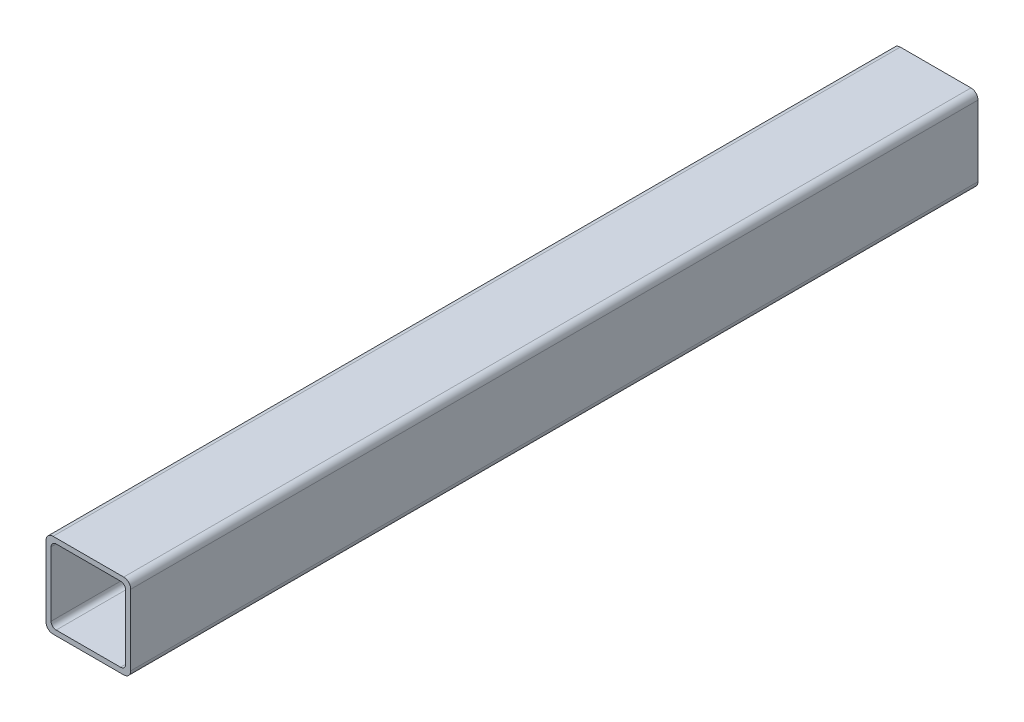
SolidWorks part; units mm, degrees
material "6061 Alloy"
ref_plane "Front Plane" through (0, 0, 0) normal (0, 0, 1) x (1, 0, 0)
ref_plane "Top Plane" through (0, 0, 0) normal (0, 1, 0) x (1, 0, 0)
ref_plane "Right Plane" through (0, 0, 0) normal (1, 0, 0) x (0, 0, -1)
ref_plane "Plane1" through (0, 0, -3683) normal (0, 0, -1) x (-1, 0, 0)
sketch "Sketch1" plane through (0, 0, -3683) normal (0, 0, -1) x (-1, 0, 0)
  line L0 (11.176, 9.652) -> (11.176, -9.652)
  line L1 (9.652, -11.176) -> (-9.652, -11.176)
  line L2 (-11.176, -9.652) -> (-11.176, 9.652)
  line L3 (-9.652, 11.176) -> (9.652, 11.176)
  line L4 (12.7, -10.5918) -> (12.7, 10.5918)
  line L5 (10.5918, 12.7) -> (-10.5918, 12.7)
  line L6 (-12.7, 10.5918) -> (-12.7, -10.5918)
  line L7 (-10.5918, -12.7) -> (10.5918, -12.7)
  arc A0 (11.176, -9.652) -> (9.652, -11.176) centre (9.652, -9.652) cw
  arc A1 (-9.652, -11.176) -> (-11.176, -9.652) centre (-9.652, -9.652) cw
  arc A2 (-11.176, 9.652) -> (-9.652, 11.176) centre (-9.652, 9.652) cw
  arc A3 (9.652, 11.176) -> (11.176, 9.652) centre (9.652, 9.652) cw
  arc A4 (12.7, 10.5918) -> (10.5918, 12.7) centre (10.5918, 10.5918) ccw
  arc A5 (-10.5918, 12.7) -> (-12.7, 10.5918) centre (-10.5918, 10.5918) ccw
  arc A6 (-12.7, -10.5918) -> (-10.5918, -12.7) centre (-10.5918, -10.5918) ccw
  arc A7 (10.5918, -12.7) -> (12.7, -10.5918) centre (10.5918, -10.5918) ccw
extrude "Boss-Extrude1" add sketch "Sketch1" against normal blind 254
